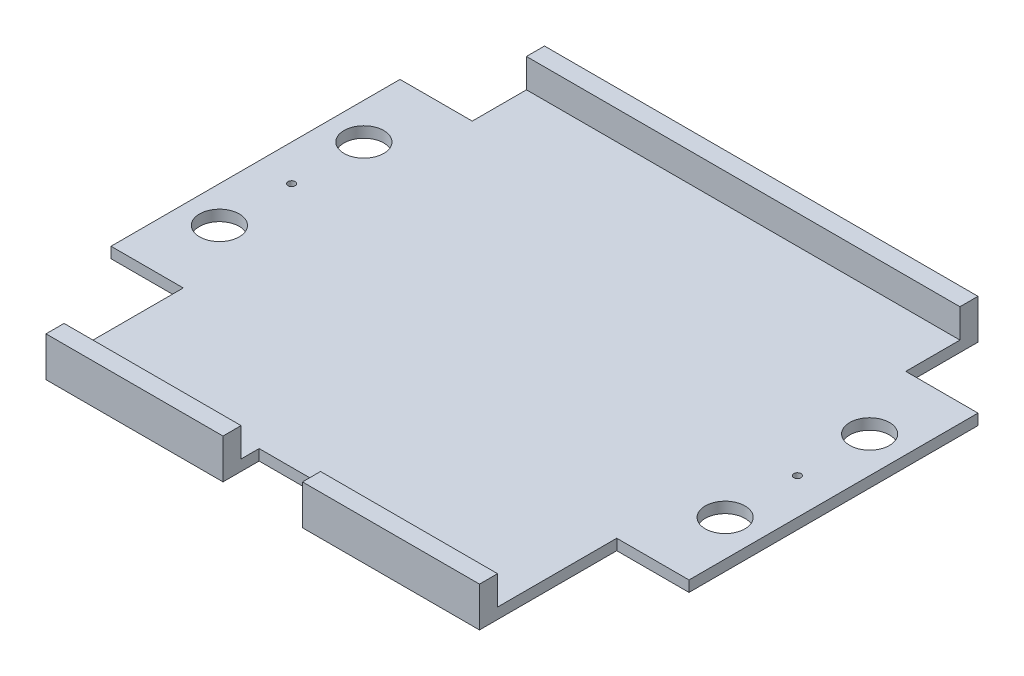
SolidWorks part; units mm, degrees
ref_plane "Front Plane" through (0, 0, 0) normal (0, 0, 1) x (1, 0, 0)
ref_plane "Top Plane" through (0, 0, 0) normal (0, 1, 0) x (1, 0, 0)
ref_plane "Right Plane" through (0, 0, 0) normal (1, 0, 0) x (0, 0, -1)
sketch "Sketch1" plane through (0, 0, 0) normal (0, 1, 0) x (1, 0, 0)
  line L1 (-60, -66.5) -> (60, -66.5)
  line L2 (-60, -66.5) -> (-60, 66.5)
  line L3 (-60, 66.5) -> (60, 66.5)
  line L4 (60, -66.5) -> (60, 66.5)
  line L5 (-60, -66.5) -> (60, 66.5) construction
  line L6 (-60, 66.5) -> (60, -66.5) construction
  point P0 (0, 0)
  dimension "D1" = 133
  dimension "D2" = 120
extrude "Boss-Extrude1" add sketch "Sketch1" along normal blind 3
sketch "Sketch2" plane through (0, 3, 0) normal (0, 1, 0) x (1, 0, 0)
  line L0 (60, -66.5) -> (60, 66.5) construction
  line L1 (-60, -66.5) -> (60, -66.5)
  line L2 (-60, -66.5) -> (-60, -61.5)
  line L3 (-60, -61.5) -> (60, -61.5)
  line L4 (60, -66.5) -> (60, -61.5)
  dimension "D1" = 5
extrude "Boss-Extrude2" add sketch "Sketch2" along normal blind 8
sketch "Sketch3" plane through (0, 11, 0) normal (0, 1, 0) x (1, 0, 0)
  line L0 (-60, -66.5) -> (60, -66.5) construction
  line L1 (-11, -66.5) -> (11, -66.5)
  line L2 (-11, -66.5) -> (-11, -56.5)
  line L3 (-11, -56.5) -> (11, -56.5)
  line L4 (11, -66.5) -> (11, -56.5)
  line L6 (-11, -66.5) -> (11, -56.5) construction
  line L8 (-11, -56.5) -> (11, -66.5) construction
  line L9 (0, 0) -> (0, -66.5) construction
  dimension "10" = 10
  dimension "D3" = 22
extrude "Cut-Extrude1" cut sketch "Sketch3" against normal through all both and the other way through all
sketch "Sketch4" plane through (0, 0, 0) normal (0, 1, 0) x (1, 0, 0)
  line L0 (60, -61.5) -> (60, 66.5) construction
  line L1 (-60, 66.5) -> (60, 66.5)
  line L2 (-60, 66.5) -> (-60, 71.5)
  line L3 (-60, 71.5) -> (60, 71.5)
  line L4 (60, 66.5) -> (60, 71.5)
  dimension "D1" = 5
extrude "Boss-Extrude3" add sketch "Sketch4" along normal blind 11
sketch "Sketch5" plane through (0, 0, 0) normal (1, 0, 0) x (0, 0, -1)
  line L0 (-61.5, 3) -> (66.5, 3) construction
  line L1 (-28.5, 3) -> (51.5, 3)
  line L2 (-28.5, 3) -> (-28.5, 0)
  line L3 (-28.5, 0) -> (51.5, 0)
  line L4 (51.5, 3) -> (51.5, 0)
  line L5 (-66.5, 0) -> (71.5, 0) construction
  line L7 (66.5, 11) -> (66.5, 3) construction
  point P8 (11.5, 3)
  dimension "D1" = 40
  dimension "D2" = 15
extrude "Boss-Extrude4" add sketch "Sketch5" along normal blind 80
sketch "Sketch6" plane through (0, 3, 0) normal (0, 1, 0) x (1, 0, 0)
  line L0 (70, 51.5) -> (70, -28.5) construction
  line L1 (80, 51.5) -> (60, 51.5) construction
  line L2 (80, -28.5) -> (60, -28.5) construction
  circle A0 centre (70, 11.5) radius 1
  circle A1 centre (70, 31.5) radius 5.5
  circle A2 centre (70, -8.5) radius 5.5
  dimension "D1" = 2
  dimension "D2" = 11
  dimension "D3" = 11
  dimension "D5" = 20
  dimension "D4" = 20
extrude "Cut-Extrude2" cut sketch "Sketch6" against normal blind 80
mirror "Mirror1" about plane through (0, 0, 0) normal (1, 0, 0) of "Cut-Extrude2", "Boss-Extrude4"
